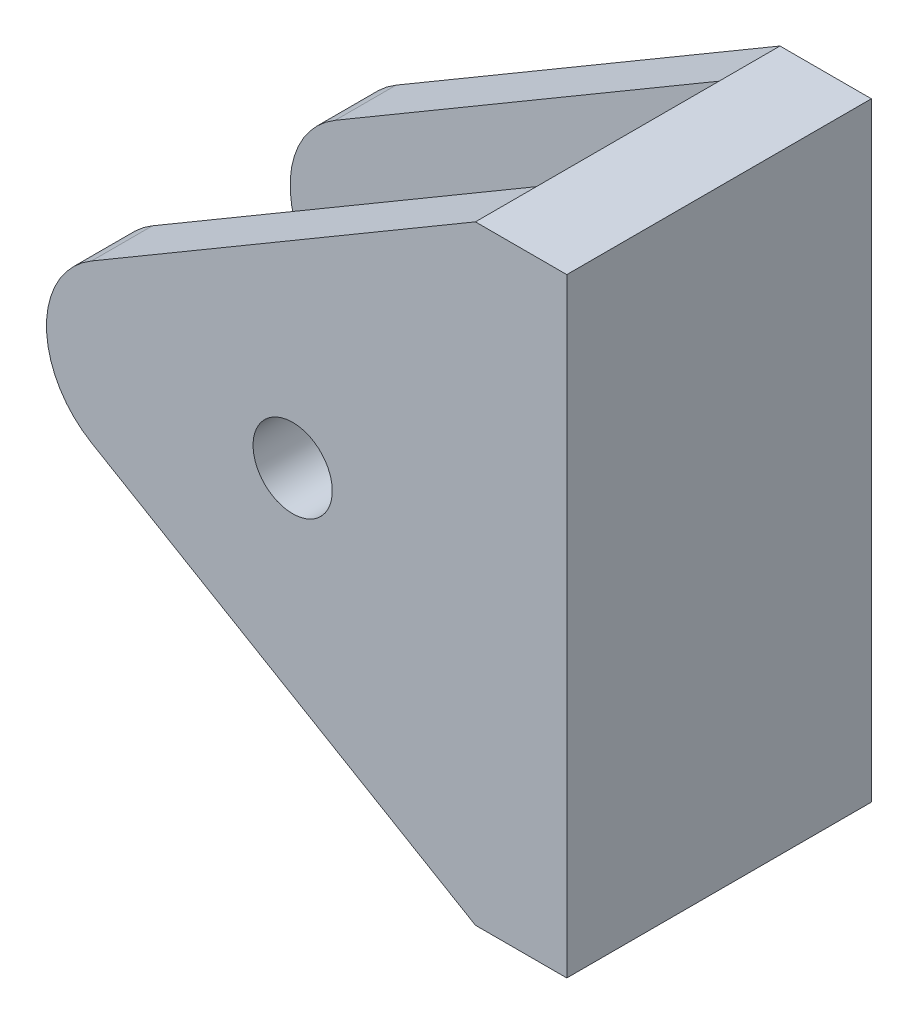
SolidWorks part; units mm, degrees
material "PLA"
ref_plane "Płaszczyzna przednia" through (0, 0, 0) normal (0, 0, 1) x (1, 0, 0)
ref_plane "Płaszczyzna górna" through (0, 0, 0) normal (0, 1, 0) x (1, 0, 0)
ref_plane "Płaszczyzna prawa" through (0, 0, 0) normal (1, 0, 0) x (0, 0, -1)
sketch "Szkic3" plane through (0, 0, 0) normal (0, 0, 1) x (1, 0, 0)
  line L7 (0, -10) -> (0, 10)
  line L8 (0, 10) -> (-3, 10)
  line L9 (-3, 10) -> (-15.6041, 2.5858)
  line L10 (0, 0) -> (33.003, 0) construction
  line L11 (0, -10) -> (-3, -10)
  line L12 (-3, -10) -> (-15.6041, -2.5858)
  arc A1 (-15.6041, -2.5858) -> (-15.6041, 2.5858) centre (-14.0831, 0) cw
  point P4 (0, 0)
  point P11 (-20, 0)
  dimension "D3" = 20
  dimension "D4" = 3
  dimension "D1" = 20
  dimension "D2" = 3
extrude "Dodanie-wyciągnięcie3" add sketch "Szkic3" along normal blind 10
ref_plane "Płaszczyzna1" through (-25, 0, 0) normal (1, 0, 0) x (0, 0, -1)
sketch "Szkic4" plane through (-25, 0, 0) normal (1, 0, 0) x (0, 0, -1)
  line L0 (0, -2.5858) -> (0, -10) construction
  line L1 (-8, 12.4569) -> (-2, 12.4569)
  line L2 (-8, 12.4569) -> (-8, -12.4569)
  line L3 (-8, -12.4569) -> (-2, -12.4569)
  line L4 (-2, 12.4569) -> (-2, -12.4569)
  line L5 (-8, 12.4569) -> (-2, -12.4569) construction
  line L6 (-8, -12.4569) -> (-2, 12.4569) construction
  line L7 (-10, -10) -> (0, -10) construction
  point P0 (-5, 0)
  dimension "D1" = 6
  dimension "D2" = 5
  dimension "D3" = 6
  dimension "D4" = 24.9139
  dimension "D5" = 10
extrude "Wytnij-wyciągnięcie2" cut sketch "Szkic4" along normal blind 22
hole_wizard "Otwór pod śrubę M21" positions "Szkic5" profile "Szkic7" hole size "M2" standard "ISO"
sketch "Szkic5" plane through (0, 0, 10) normal (0, 0, 1) x (1, 0, 0)
  line L0 (0, -10) -> (0, 10) construction
  point P0 (-9, 0)
  point P5 (0, 0)
  dimension "D1" = 9
sketch "Szkic7" plane through (-9, 0, 10) normal (1, 0, 0) x (0, -1, 0)
  line L0 (0, 0) -> (0, 10.7801)
  line L1 (0, 10.7801) -> (1.3, 9.999)
  line L2 (1.3, 9.999) -> (1.3, 0)
  line L5 (1.3, 0) -> (0, 0)
  line L10 (0, 10.7801) -> (-1.3, 9.999) construction
  line L11 (0, -6.35) -> (0, 107.95) construction
  dimension "Średnica otworu" = 2.6
  dimension "Głębokość otworu" = 9.999
  dimension "Kąt wiertła" = 118
ref_plane "Blat stołu" through (0, 0, 0) normal (1, 0, 0) x (0, 0, -1)
